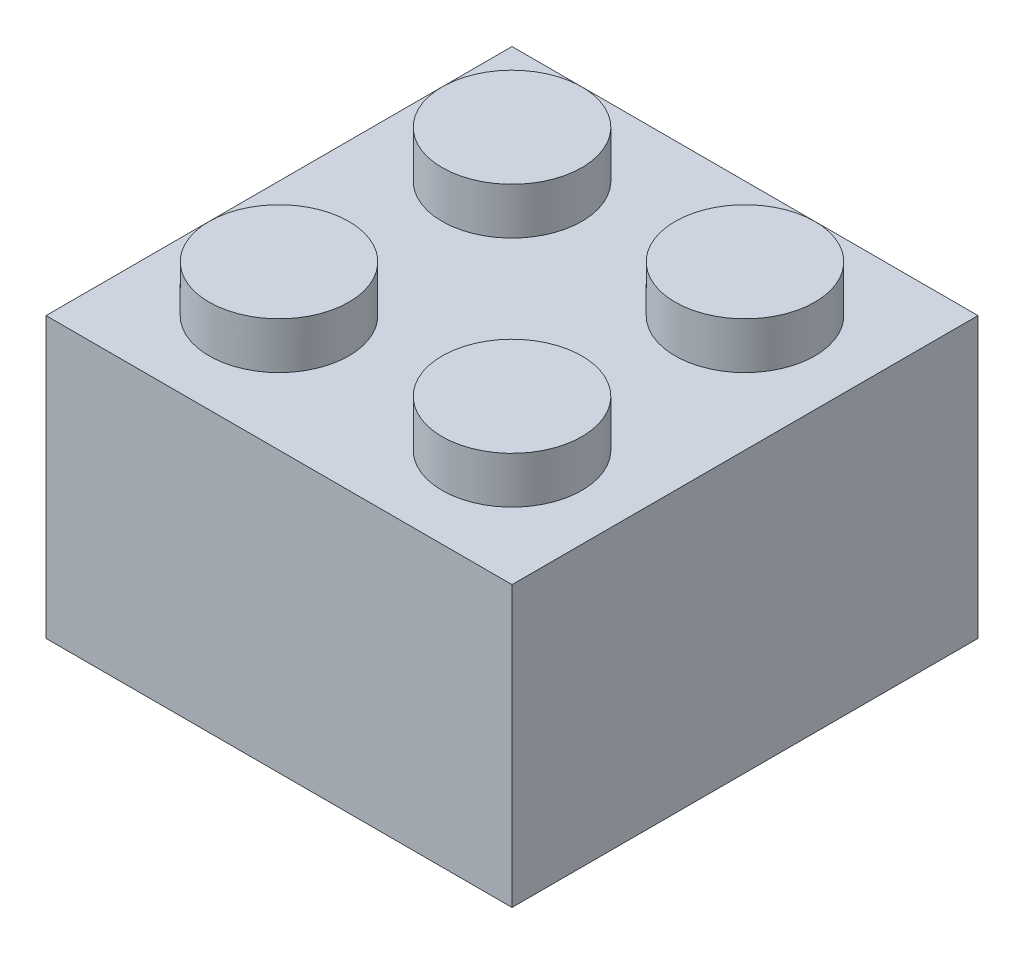
SolidWorks part; units mm, degrees
ref_plane "Front Plane" through (0, 0, 0) normal (0, 0, 1) x (1, 0, 0)
ref_plane "Top Plane" through (0, 0, 0) normal (0, 1, 0) x (1, 0, 0)
ref_plane "Right Plane" through (0, 0, 0) normal (1, 0, 0) x (0, 0, -1)
sketch "Sketch1" plane through (0, 0, 0) normal (0, 1, 0) x (1, 0, 0)
  line L1 (0, 0) -> (10, 0)
  line L2 (0, 0) -> (0, 10)
  line L3 (0, 10) -> (10, 10)
  line L4 (10, 0) -> (10, 10)
  line L5 (1, 1) -> (9, 1)
  line L6 (1, 1) -> (1, 9)
  line L7 (1, 9) -> (9, 9)
  line L8 (9, 1) -> (9, 9)
  point P9 (0, 5)
  point P10 (1, 5)
  point P11 (5, 1)
  point P12 (5, 0)
  dimension "D1" = 10
  dimension "D2" = 1
extrude "Boss-Extrude1" add sketch "Sketch1" along normal blind 6
sketch "Sketch2" plane through (0, 0, -9) normal (0, 0, 1) x (1, 0, 0)
  line L0 (9, 6) -> (9, 0) construction
  line L1 (1, 6) -> (9, 6)
  line L2 (1, 6) -> (1, 5)
  line L3 (1, 5) -> (9, 5)
  line L4 (9, 6) -> (9, 5)
  dimension "D1" = 1
extrude "Boss-Extrude2" add sketch "Sketch2" along normal up to next
sketch "Sketch3" plane through (0, 6, 0) normal (0, 1, 0) x (1, 0, 0)
  line L0 (2.5, 2.5) -> (2.5, 7.5)
  line L1 (0, 0) -> (2.5, 0)
  line L2 (0, 0) -> (0, 2.5)
  line L3 (0, 2.5) -> (2.5, 2.5)
  line L4 (2.5, 0) -> (2.5, 2.5)
  line L6 (0, 5) -> (10, 5)
  line L7 (0, 10) -> (0, 0) construction
  line L8 (10, 0) -> (10, 10) construction
  line L9 (5, 10) -> (5, 0)
  line L10 (10, 10) -> (0, 10) construction
  line L11 (0, 0) -> (10, 0) construction
  circle A0 centre (2.5, 2.5) radius 1.5
  circle A1 centre (7.5, 2.5) radius 1.5
  circle A2 centre (7.5, 7.5) radius 1.5
  circle A3 centre (2.5, 7.5) radius 1.5
  dimension "D2" = 3
  dimension "D1" = 2.5
extrude "Boss-Extrude3" add sketch "Sketch3" along normal blind 1
sketch "Sketch4" plane through (0, 5, 0) normal (0, -1, 0) x (-1, 0, 0)
  line L0 (-1, 5) -> (-9, 5)
  line L1 (-1, 9) -> (-9, 9)
  line L2 (-1, 9) -> (-1, 1)
  line L3 (-1, 1) -> (-9, 1)
  line L4 (-9, 9) -> (-9, 1)
  line L5 (-5, 1) -> (-5, 9)
  line L7 (-5, 5) -> (-7.5, 5)
  line L8 (-5, 5) -> (-5, 7.5)
  line L9 (-5, 7.5) -> (-7.5, 7.5)
  line L10 (-7.5, 5) -> (-7.5, 7.5)
  circle A0 centre (-5, 5) radius 2.0355
  circle A1 centre (-7.5, 7.5) radius 1.5
  circle A2 centre (-5, 5) radius 1.5
  circle A3 centre (-7.5, 7.5) radius 0.75
  dimension "D1" = 2.5
  dimension "D2" = 3
  dimension "D3" = 1.5
extrude "Boss-Extrude4" add sketch "Sketch4" along normal up to surface (5 mm away) contours A2 L0 A0 L8 | A2 L5 A0 L0 | A2 L7 A0 L5 | A2 L8 A0 L7 up to face at (5, 0, -5)
sketch "Sketch5" plane through (0, 5, 0) normal (0, -1, 0) x (-1, 0, 0)
  line L0 (-9, 1) -> (-9, 9) construction
  line L1 (-9, 9) -> (-1, 9)
  line L2 (-9, 9) -> (-9, 1)
  line L3 (-9, 1) -> (-1, 1)
  line L4 (-1, 9) -> (-1, 1)
  line L5 (-1, 9) -> (-9, 9) construction
  line L6 (-1, 1) -> (-1, 9) construction
  line L7 (-5, 1) -> (-5, 9)
  line L8 (-9, 5) -> (-1, 5)
  line L10 (-5, 5) -> (-7.5, 5)
  line L11 (-5, 5) -> (-5, 7.5)
  line L12 (-5, 7.5) -> (-7.5, 7.5)
  line L13 (-7.5, 5) -> (-7.5, 7.5)
  circle A0 centre (-7.5, 7.5) radius 0.75
  circle A1 centre (-2.5, 7.5) radius 0.75
  circle A2 centre (-2.5, 2.5) radius 0.75
  circle A3 centre (-7.5, 2.5) radius 0.75
  dimension "D2" = 1.5
  dimension "D1" = 2.5
extrude "Cut-Extrude2" cut sketch "Sketch5" against normal blind 1 contours L12 A0 L13 | L13 A0 L12 | A1 | A2 | A3
equation "\"u\"=38.7423"
